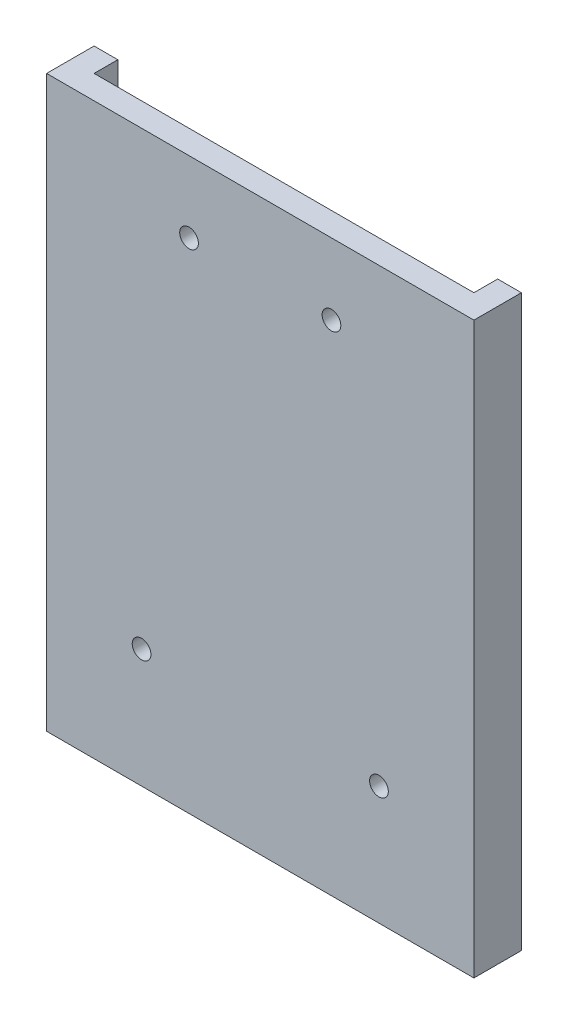
SolidWorks part; units mm, degrees
material "ABS"
ref_plane "Front" through (0, 0, 0) normal (0, 0, 1) x (1, 0, 0)
ref_plane "Top" through (0, 0, 0) normal (0, 1, 0) x (1, 0, 0)
ref_plane "Right" through (0, 0, 0) normal (1, 0, 0) x (0, 0, -1)
sketch "Sketch1" plane through (0, 0, 0) normal (0, 1, 0) x (1, 0, 0)
  line L1 (-28.575, 3.175) -> (28.575, 3.175)
  line L2 (-28.575, 3.175) -> (-28.575, -3.175)
  line L3 (-28.575, -3.175) -> (28.575, -3.175)
  line L4 (28.575, 3.175) -> (28.575, -3.175)
  line L5 (-28.575, 3.175) -> (28.575, -3.175) construction
  line L6 (-28.575, -3.175) -> (28.575, 3.175) construction
  point P0 (0, 0)
  dimension "D1" = 57.15
  dimension "D2" = 6.35
extrude "Boss-Extrude1" add sketch "Sketch1" along normal blind 76.2
sketch "Sketch2" plane through (0, 76.2, 0) normal (0, 1, 0) x (1, 0, 0)
  line L0 (28.575, 3.175) -> (-28.575, 3.175) construction
  line L1 (-25.4, 3.175) -> (25.4, 3.175)
  line L2 (-25.4, 3.175) -> (-25.4, 0)
  line L3 (-25.4, 0) -> (25.4, 0)
  line L4 (25.4, 3.175) -> (25.4, 0)
  dimension "D1" = 50.8
extrude "Cut-Extrude1" cut sketch "Sketch2" against normal offset from surface (73.025 mm away) 3.175 up to face at (0, 0, 0)
sketch "Sketch4" plane through (0, 0, 0) normal (0, 0, -1) x (-1, 0, 0)
  line L0 (-25.4, 15.875) -> (25.4, 15.875) construction
  line L1 (-25.4, 3.175) -> (-25.4, 76.2) construction
  line L2 (25.4, 3.175) -> (25.4, 76.2) construction
  line L3 (-25.4, 66.675) -> (25.4, 66.675) construction
  line L4 (25.4, 3.175) -> (25.4, 76.2) construction
  line L5 (-25.4, 3.175) -> (25.4, 3.175) construction
  line L6 (-15.875, 15.875) -> (-9.525, 66.675) construction
  line L7 (9.525, 66.675) -> (15.875, 15.875) construction
  line L8 (-12.7, 41.275) -> (12.7, 41.275) construction
  circle A0 centre (-9.525, 66.675) radius 1.25
  circle A1 centre (9.525, 66.675) radius 1.25
  circle A2 centre (-15.875, 15.875) radius 1.25
  circle A3 centre (15.875, 15.875) radius 1.25
  point P20 (0, 66.675)
  point P23 (0, 41.275)
  point P24 (0, 0)
  dimension "D3" = 2.5
  dimension "D1" = 50.8
  dimension "D2" = 12.7
  dimension "D4" = 19.05
  dimension "D5" = 31.75
extrude "Cut-Extrude2" cut sketch "Sketch4" against normal through all
